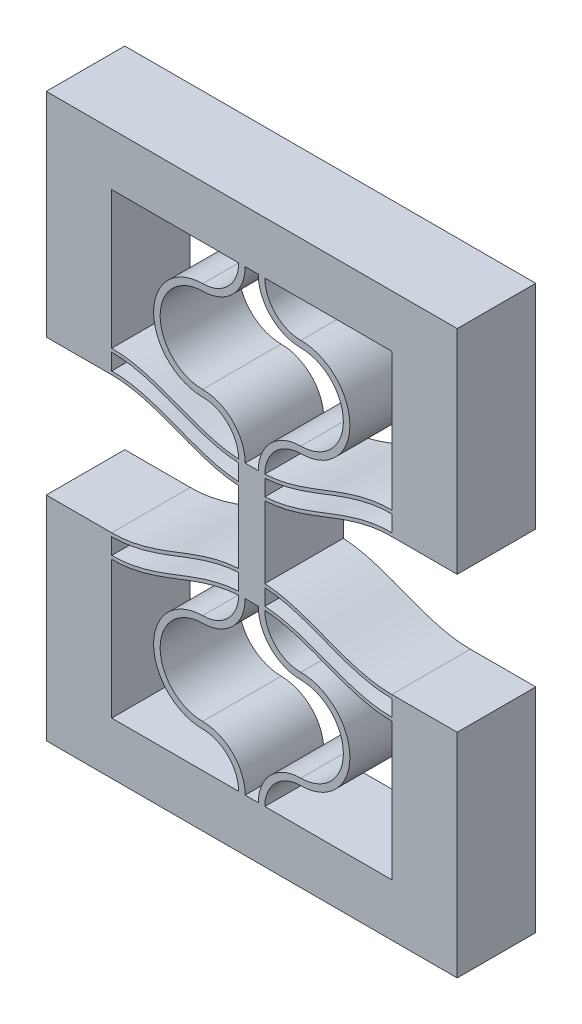
SolidWorks part; units mm, degrees
ref_plane "Front Plane" through (0, 0, 0) normal (0, 0, 1) x (1, 0, 0)
ref_plane "Top Plane" through (0, 0, 0) normal (0, 1, 0) x (1, 0, 0)
ref_plane "Right Plane" through (0, 0, 0) normal (1, 0, 0) x (0, 0, -1)
sketch "Sketch1" plane through (0, 0, 0) normal (0, 0, 1) x (1, 0, 0)
  line L4 (0, 10.5) -> (0, 0)
  line L5 (10.2, 0) -> (10.2, 13) construction
  line L6 (10.2, 13) -> (10.2, 15.9852) construction
  line L17 (9.7, 0) -> (0, 0)
  line L18 (10.7, 0) -> (20.4, 0)
  line L19 (20.4, 0) -> (20.4, 10.5)
  line L20 (10.7, 13.2452) -> (10.7, 14.4852)
  line L21 (9.7, 13.2452) -> (9.7, 14.4852)
  line L22 (10.7, 14.7452) -> (10.7, 15.9852)
  line L23 (10.7, 15.9852) -> (9.7, 15.9852)
  line L24 (9.7, 15.9852) -> (9.7, 14.7452)
  line L31 (-5, 12.26) -> (-5, -4)
  line L32 (-5, -4) -> (25.4, -4)
  line L33 (25.4, -4) -> (25.4, 12.26)
  line L34 (0, 10.76) -> (0, 12)
  line L36 (-5, 12.26) -> (0, 12.26)
  line L37 (25.4, 12.26) -> (20.4, 12.26)
  line L38 (20.4, 10.76) -> (20.4, 12)
  arc A0 (10.2, 13) -> (6.95, 9.75) centre (6.95, 13) cw
  arc A1 (6.95, 9.75) -> (6.95, 3.25) centre (6.95, 6.5) ccw
  arc A2 (6.95, 3.25) -> (10.2, 0) centre (6.95, 0) cw
  arc A3 (9.7, 12.9852) -> (6.95, 10.25) centre (6.95, 13) cw
  arc A4 (6.95, 10.25) -> (6.95, 2.75) centre (6.95, 6.5) ccw
  arc A5 (6.95, 2.75) -> (9.7, 0) centre (6.95, 0) cw
  arc A6 (9.7, 13) -> (6.95, 10.25) centre (6.95, 13) cw construction
  arc A7 (13.45, 3.25) -> (10.2, 0) centre (13.45, 0) ccw
  arc A8 (13.45, 2.75) -> (10.7, 0) centre (13.45, 0) ccw
  arc A9 (13.45, 9.75) -> (13.45, 3.25) centre (13.45, 6.5) cw
  arc A10 (13.45, 10.25) -> (13.45, 2.75) centre (13.45, 6.5) cw
  arc A11 (10.7, 12.9852) -> (13.45, 10.25) centre (13.45, 13) ccw
  arc A12 (10.2, 13) -> (13.45, 9.75) centre (13.45, 13) ccw
  spline S0 degree 4 poles (-2.0399, 10.9987) (-1.9769, 10.9844) (-1.8506, 10.9568) (-1.6594, 10.9185) (-1.4063, 10.8738) (-1.1473, 10.836) (-0.8994, 10.8056) (-0.6275, 10.7825) (-0.4084, 10.7671) (-0.0945, 10.7598) (0.0489, 10.7593) (0.3554, 10.7653) (0.5833, 10.7785) (0.8327, 10.7992) (1.1232, 10.8326) (1.4148, 10.8743) (1.7521, 10.9345) (2.2064, 11.0333) (2.726, 11.1697) (3.2397, 11.3281) (3.7479, 11.5024) (4.1845, 11.6613) (4.5513, 11.7992) (4.9172, 11.9395) (5.2828, 12.0805) (5.7402, 12.2559) (6.427, 12.5125) (7.2136, 12.7819) (8.1107, 13.0284) (9.0261, 13.1932) (9.8075, 13.2661) (10.5925, 13.2661) (11.3739, 13.1932) (12.2893, 13.0284) (13.1864, 12.7819) (13.973, 12.5125) (14.6598, 12.2559) (15.2087, 12.0455) (15.6656, 11.8688) (16.1235, 11.6948) (16.6521, 11.5024) (17.1603, 11.3281) (17.6739, 11.1697) (18.1937, 11.0333) (18.5999, 10.9449) (18.8889, 10.8915) (19.1309, 10.8534) (19.3251, 10.827) (19.5196, 10.8048) (19.7158, 10.7868) (19.909, 10.7733) (20.1017, 10.7642) (20.3513, 10.7593) (20.4943, 10.7598) (20.8085, 10.7671) (21.0274, 10.7825) (21.2994, 10.8056) (21.5473, 10.836) (21.8063, 10.8738) (22.0594, 10.9185) (22.2506, 10.9568) (22.3769, 10.9844) (22.4399, 10.9987) knots 0 0 0 0 0 0.010251 0.020502 0.030753 0.041005 0.05113 0.061255 0.071381 0.081506 0.089265 0.097024 0.112543 0.120302 0.128061 0.143579 0.159098 0.174616 0.201648 0.22868 0.244198 0.259716 0.275235 0.290753 0.306271 0.32179 0.352826 0.40689 0.437927 0.468963 0.5 0.531037 0.562073 0.59311 0.647174 0.67821 0.693729 0.709247 0.740284 0.755802 0.77132 0.798352 0.825384 0.840902 0.856421 0.86418 0.871939 0.879698 0.887457 0.895217 0.902976 0.910735 0.918494 0.928619 0.938745 0.94887 0.958995 0.969247 0.979498 0.989749 1 1 1 1 1 construction
  spline S1 degree 4 poles (0, 10.76) (0.041, 10.76) (0.1243, 10.7608) (0.3554, 10.7653) (0.5833, 10.7785) (0.8327, 10.7992) (1.1232, 10.8326) (1.4148, 10.8743) (1.7521, 10.9345) (2.2064, 11.0333) (2.726, 11.1697) (3.2397, 11.3281) (3.7479, 11.5024) (4.1845, 11.6613) (4.5513, 11.7992) (4.9172, 11.9395) (5.2828, 12.0805) (5.7402, 12.2559) (6.427, 12.5125) (7.2136, 12.7819) (8.1107, 13.0284) (9.0261, 13.1932) (9.8075, 13.2661) (10.5925, 13.2661) (11.3739, 13.1932) (12.2893, 13.0284) (13.1864, 12.7819) (13.973, 12.5125) (14.6598, 12.2559) (15.2087, 12.0455) (15.6656, 11.8688) (16.1235, 11.6948) (16.6521, 11.5024) (17.1603, 11.3281) (17.6739, 11.1697) (18.1937, 11.0333) (18.5999, 10.9449) (18.8889, 10.8915) (19.1309, 10.8534) (19.3251, 10.827) (19.5196, 10.8048) (19.7158, 10.7868) (19.909, 10.7733) (20.1017, 10.7642) (20.2757, 10.7608) (20.359, 10.76) (20.4, 10.76) knots 0.081506 0.081506 0.081506 0.081506 0.081506 0.089265 0.097024 0.112543 0.120302 0.128061 0.143579 0.159098 0.174616 0.201648 0.22868 0.244198 0.259716 0.275235 0.290753 0.306271 0.32179 0.352826 0.40689 0.437927 0.468963 0.5 0.531037 0.562073 0.59311 0.647174 0.67821 0.693729 0.709247 0.740284 0.755802 0.77132 0.798352 0.825384 0.840902 0.856421 0.86418 0.871939 0.879698 0.887457 0.895217 0.902976 0.910735 0.918494 0.918494 0.918494 0.918494 0.918494
  spline S2 degree 4 poles (-2.0399, 12.2387) (-1.9769, 12.2244) (-1.8506, 12.1968) (-1.6594, 12.1585) (-1.4063, 12.1138) (-1.1473, 12.076) (-0.8994, 12.0456) (-0.6275, 12.0225) (-0.4084, 12.0071) (-0.0945, 11.9998) (0.0489, 11.9993) (0.3554, 12.0053) (0.5833, 12.0185) (0.8327, 12.0392) (1.1232, 12.0726) (1.4148, 12.1143) (1.7521, 12.1745) (2.2064, 12.2733) (2.726, 12.4097) (3.2397, 12.5681) (3.7479, 12.7424) (4.1845, 12.9013) (4.5513, 13.0392) (4.9172, 13.1795) (5.2828, 13.3205) (5.7402, 13.4959) (6.427, 13.7525) (7.2136, 14.0219) (8.1107, 14.2684) (9.0261, 14.4332) (9.8075, 14.5061) (10.5925, 14.5061) (11.3739, 14.4332) (12.2893, 14.2684) (13.1864, 14.0219) (13.973, 13.7525) (14.6598, 13.4959) (15.2087, 13.2855) (15.6656, 13.1088) (16.1235, 12.9348) (16.6521, 12.7424) (17.1603, 12.5681) (17.6739, 12.4097) (18.1937, 12.2733) (18.5999, 12.1849) (18.8889, 12.1315) (19.1309, 12.0934) (19.3251, 12.067) (19.5196, 12.0448) (19.7158, 12.0268) (19.909, 12.0133) (20.1017, 12.0042) (20.3513, 11.9993) (20.4943, 11.9998) (20.8085, 12.0071) (21.0274, 12.0225) (21.2994, 12.0456) (21.5473, 12.076) (21.8063, 12.1138) (22.0594, 12.1585) (22.2506, 12.1968) (22.3769, 12.2244) (22.4399, 12.2387) knots 0 0 0 0 0 0.010251 0.020502 0.030753 0.041005 0.05113 0.061255 0.071381 0.081506 0.089265 0.097024 0.112543 0.120302 0.128061 0.143579 0.159098 0.174616 0.201648 0.22868 0.244198 0.259716 0.275235 0.290753 0.306271 0.32179 0.352826 0.40689 0.437927 0.468963 0.5 0.531037 0.562073 0.59311 0.647174 0.67821 0.693729 0.709247 0.740284 0.755802 0.77132 0.798352 0.825384 0.840902 0.856421 0.86418 0.871939 0.879698 0.887457 0.895217 0.902976 0.910735 0.918494 0.928619 0.938745 0.94887 0.958995 0.969247 0.979498 0.989749 1 1 1 1 1 construction
  spline S3 degree 4 poles (0, 12) (0.041, 12) (0.1243, 12.0008) (0.3554, 12.0053) (0.5833, 12.0185) (0.8327, 12.0392) (1.1232, 12.0726) (1.4148, 12.1143) (1.7521, 12.1745) (2.2064, 12.2733) (2.726, 12.4097) (3.2397, 12.5681) (3.7479, 12.7424) (4.1845, 12.9013) (4.5513, 13.0392) (4.9172, 13.1795) (5.2828, 13.3205) (5.7402, 13.4959) (6.427, 13.7525) (7.2136, 14.0219) (8.1107, 14.2684) (9.0261, 14.4332) (9.8075, 14.5061) (10.5925, 14.5061) (11.3739, 14.4332) (12.2893, 14.2684) (13.1864, 14.0219) (13.973, 13.7525) (14.6598, 13.4959) (15.2087, 13.2855) (15.6656, 13.1088) (16.1235, 12.9348) (16.6521, 12.7424) (17.1603, 12.5681) (17.6739, 12.4097) (18.1937, 12.2733) (18.5999, 12.1849) (18.8889, 12.1315) (19.1309, 12.0934) (19.3251, 12.067) (19.5196, 12.0448) (19.7158, 12.0268) (19.909, 12.0133) (20.1017, 12.0042) (20.2757, 12.0008) (20.359, 12) (20.4, 12) knots 0.081506 0.081506 0.081506 0.081506 0.081506 0.089265 0.097024 0.112543 0.120302 0.128061 0.143579 0.159098 0.174616 0.201648 0.22868 0.244198 0.259716 0.275235 0.290753 0.306271 0.32179 0.352826 0.40689 0.437927 0.468963 0.5 0.531037 0.562073 0.59311 0.647174 0.67821 0.693729 0.709247 0.740284 0.755802 0.77132 0.798352 0.825384 0.840902 0.856421 0.86418 0.871939 0.879698 0.887457 0.895217 0.902976 0.910735 0.918494 0.918494 0.918494 0.918494 0.918494
  spline S4 degree 4 poles (-2.0399, 12.4987) (-1.9769, 12.4844) (-1.8506, 12.4568) (-1.6594, 12.4185) (-1.4063, 12.3738) (-1.1473, 12.336) (-0.8994, 12.3056) (-0.6275, 12.2825) (-0.4084, 12.2671) (-0.0945, 12.2598) (0.0489, 12.2593) (0.3554, 12.2653) (0.5833, 12.2785) (0.8327, 12.2992) (1.1232, 12.3326) (1.4148, 12.3743) (1.7521, 12.4345) (2.2064, 12.5333) (2.726, 12.6697) (3.2397, 12.8281) (3.7479, 13.0024) (4.1845, 13.1613) (4.5513, 13.2992) (4.9172, 13.4395) (5.2828, 13.5805) (5.7402, 13.7559) (6.427, 14.0125) (7.2136, 14.2819) (8.1107, 14.5284) (9.0261, 14.6932) (9.8075, 14.7661) (10.5925, 14.7661) (11.3739, 14.6932) (12.2893, 14.5284) (13.1864, 14.2819) (13.973, 14.0125) (14.6598, 13.7559) (15.2087, 13.5455) (15.6656, 13.3688) (16.1235, 13.1948) (16.6521, 13.0024) (17.1603, 12.8281) (17.6739, 12.6697) (18.1937, 12.5333) (18.5999, 12.4449) (18.8889, 12.3915) (19.1309, 12.3534) (19.3251, 12.327) (19.5196, 12.3048) (19.7158, 12.2868) (19.909, 12.2733) (20.1017, 12.2642) (20.3513, 12.2593) (20.4943, 12.2598) (20.8085, 12.2671) (21.0274, 12.2825) (21.2994, 12.3056) (21.5473, 12.336) (21.8063, 12.3738) (22.0594, 12.4185) (22.2506, 12.4568) (22.3769, 12.4844) (22.4399, 12.4987) knots 0 0 0 0 0 0.010251 0.020502 0.030753 0.041005 0.05113 0.061255 0.071381 0.081506 0.089265 0.097024 0.112543 0.120302 0.128061 0.143579 0.159098 0.174616 0.201648 0.22868 0.244198 0.259716 0.275235 0.290753 0.306271 0.32179 0.352826 0.40689 0.437927 0.468963 0.5 0.531037 0.562073 0.59311 0.647174 0.67821 0.693729 0.709247 0.740284 0.755802 0.77132 0.798352 0.825384 0.840902 0.856421 0.86418 0.871939 0.879698 0.887457 0.895217 0.902976 0.910735 0.918494 0.928619 0.938745 0.94887 0.958995 0.969247 0.979498 0.989749 1 1 1 1 1 construction
  spline S5 degree 4 poles (0, 12.26) (0.041, 12.26) (0.1243, 12.2608) (0.3554, 12.2653) (0.5833, 12.2785) (0.8327, 12.2992) (1.1232, 12.3326) (1.4148, 12.3743) (1.7521, 12.4345) (2.2064, 12.5333) (2.726, 12.6697) (3.2397, 12.8281) (3.7479, 13.0024) (4.1845, 13.1613) (4.5513, 13.2992) (4.9172, 13.4395) (5.2828, 13.5805) (5.7402, 13.7559) (6.427, 14.0125) (7.2136, 14.2819) (8.1107, 14.5284) (9.0261, 14.6932) (9.8075, 14.7661) (10.5925, 14.7661) (11.3739, 14.6932) (12.2893, 14.5284) (13.1864, 14.2819) (13.973, 14.0125) (14.6598, 13.7559) (15.2087, 13.5455) (15.6656, 13.3688) (16.1235, 13.1948) (16.6521, 13.0024) (17.1603, 12.8281) (17.6739, 12.6697) (18.1937, 12.5333) (18.5999, 12.4449) (18.8889, 12.3915) (19.1309, 12.3534) (19.3251, 12.327) (19.5196, 12.3048) (19.7158, 12.2868) (19.909, 12.2733) (20.1017, 12.2642) (20.2757, 12.2608) (20.359, 12.26) (20.4, 12.26) knots 0.081506 0.081506 0.081506 0.081506 0.081506 0.089265 0.097024 0.112543 0.120302 0.128061 0.143579 0.159098 0.174616 0.201648 0.22868 0.244198 0.259716 0.275235 0.290753 0.306271 0.32179 0.352826 0.40689 0.437927 0.468963 0.5 0.531037 0.562073 0.59311 0.647174 0.67821 0.693729 0.709247 0.740284 0.755802 0.77132 0.798352 0.825384 0.840902 0.856421 0.86418 0.871939 0.879698 0.887457 0.895217 0.902976 0.910735 0.918494 0.918494 0.918494 0.918494 0.918494
  spline S8 degree 4 poles (-2.0399, 10.7387) (-1.9769, 10.7244) (-1.8506, 10.6968) (-1.6594, 10.6585) (-1.4063, 10.6138) (-1.1473, 10.576) (-0.8994, 10.5456) (-0.6275, 10.5225) (-0.4084, 10.5071) (-0.0945, 10.4998) (0.0489, 10.4993) (0.3554, 10.5053) (0.5833, 10.5185) (0.8327, 10.5392) (1.1232, 10.5726) (1.4148, 10.6143) (1.7521, 10.6745) (2.2064, 10.7733) (2.726, 10.9097) (3.2397, 11.0681) (3.7479, 11.2424) (4.1845, 11.4013) (4.5513, 11.5392) (4.9172, 11.6795) (5.2828, 11.8205) (5.7402, 11.9959) (6.427, 12.2525) (7.2136, 12.5219) (8.1107, 12.7684) (9.0261, 12.9332) (9.8075, 13.0061) (10.5925, 13.0061) (11.3739, 12.9332) (12.2893, 12.7684) (13.1864, 12.5219) (13.973, 12.2525) (14.6598, 11.9959) (15.2087, 11.7855) (15.6656, 11.6088) (16.1235, 11.4348) (16.6521, 11.2424) (17.1603, 11.0681) (17.6739, 10.9097) (18.1937, 10.7733) (18.5999, 10.6849) (18.8889, 10.6315) (19.1309, 10.5934) (19.3251, 10.567) (19.5196, 10.5448) (19.7158, 10.5268) (19.909, 10.5133) (20.1017, 10.5042) (20.3513, 10.4993) (20.4943, 10.4998) (20.8085, 10.5071) (21.0274, 10.5225) (21.2994, 10.5456) (21.5473, 10.576) (21.8063, 10.6138) (22.0594, 10.6585) (22.2506, 10.6968) (22.3769, 10.7244) (22.4399, 10.7387) knots 0 0 0 0 0 0.010251 0.020502 0.030753 0.041005 0.05113 0.061255 0.071381 0.081506 0.089265 0.097024 0.112543 0.120302 0.128061 0.143579 0.159098 0.174616 0.201648 0.22868 0.244198 0.259716 0.275235 0.290753 0.306271 0.32179 0.352826 0.40689 0.437927 0.468963 0.5 0.531037 0.562073 0.59311 0.647174 0.67821 0.693729 0.709247 0.740284 0.755802 0.77132 0.798352 0.825384 0.840902 0.856421 0.86418 0.871939 0.879698 0.887457 0.895217 0.902976 0.910735 0.918494 0.928619 0.938745 0.94887 0.958995 0.969247 0.979498 0.989749 1 1 1 1 1 construction
  spline S9 degree 4 poles (0, 10.5) (0.041, 10.5) (0.1243, 10.5008) (0.3554, 10.5053) (0.5833, 10.5185) (0.8327, 10.5392) (1.1232, 10.5726) (1.4148, 10.6143) (1.7521, 10.6745) (2.2064, 10.7733) (2.726, 10.9097) (3.2397, 11.0681) (3.7479, 11.2424) (4.1845, 11.4013) (4.5513, 11.5392) (4.9172, 11.6795) (5.2828, 11.8205) (5.7402, 11.9959) (6.427, 12.2525) (7.2136, 12.5219) (8.1107, 12.7684) (9.0261, 12.9332) (9.8075, 13.0061) (10.5925, 13.0061) (11.3739, 12.9332) (12.2893, 12.7684) (13.1864, 12.5219) (13.973, 12.2525) (14.6598, 11.9959) (15.2087, 11.7855) (15.6656, 11.6088) (16.1235, 11.4348) (16.6521, 11.2424) (17.1603, 11.0681) (17.6739, 10.9097) (18.1937, 10.7733) (18.5999, 10.6849) (18.8889, 10.6315) (19.1309, 10.5934) (19.3251, 10.567) (19.5196, 10.5448) (19.7158, 10.5268) (19.909, 10.5133) (20.1017, 10.5042) (20.2757, 10.5008) (20.359, 10.5) (20.4, 10.5) knots 0.081506 0.081506 0.081506 0.081506 0.081506 0.089265 0.097024 0.112543 0.120302 0.128061 0.143579 0.159098 0.174616 0.201648 0.22868 0.244198 0.259716 0.275235 0.290753 0.306271 0.32179 0.352826 0.40689 0.437927 0.468963 0.5 0.531037 0.562073 0.59311 0.647174 0.67821 0.693729 0.709247 0.740284 0.755802 0.77132 0.798352 0.825384 0.840902 0.856421 0.86418 0.871939 0.879698 0.887457 0.895217 0.902976 0.910735 0.918494 0.918494 0.918494 0.918494 0.918494
  dimension "D4" = 0.26
  dimension "D6" = 4
  dimension "D1" = 13
  dimension "D2" = 0.5
  dimension "D3" = 0.26
  dimension "D7" = 5
  dimension "D5" = 1.5
extrude "Boss-Extrude1" add sketch "Sketch1" along normal blind 6
sketch "Sketch4" plane through (0, 15.9852, 0) normal (0, 1, 0) x (1, 0, 0)
  line L24 (10.7, 0) -> (9.7, 0)
  line L25 (9.7, 0) -> (9.7, -6)
  line L26 (10.7, 0) -> (9.7, 0)
  line L27 (10.7, -6) -> (10.7, 0)
  line L29 (9.7, 0) -> (9.7, -6)
  line L31 (10.7, -6) -> (10.7, 0)
  line L32 (9.7, -6) -> (10.7, -6)
  line L33 (9.7, -6) -> (10.7, -6)
  dimension "D1" = 0
extrude "Boss-Extrude2" add sketch "Sketch4" along normal blind 1.5
mirror "Mirror3" about plane through (0, 17.4852, 0) normal (0, 1, 0) of bodies 179
ref_plane "Plane1" through (10.2, 0, 0) normal (-1, 0, 0) x (0, 0, 1)
split "Split2" trim tools "Plane1" bodies to split 247 102 resulting bodies 225
sketch "Sketch7" plane through (10.2, 0, 0) normal (-1, 0, 0) x (0, 0, 1)
  line L4 (6, 34.9704) -> (6, 38.9704)
  line L12 (0, 13) -> (6, 13)
  line L13 (0, 13) -> (6, 13)
  line L14 (6, 13) -> (6, 21.9704)
  line L15 (6, 13) -> (6, 21.9704)
  line L20 (6, 0) -> (0, 0)
  line L22 (6, 0) -> (0, 0)
  line L23 (0, -4) -> (6, -4)
  line L27 (0, -4) -> (6, -4)
  line L31 (6, 21.9704) -> (0, 21.9704)
  line L32 (6, 21.9704) -> (0, 21.9704)
  line L33 (0, 21.9704) -> (0, 13)
  line L34 (0, 21.9704) -> (0, 13)
  line L36 (6, -4) -> (6, 0)
  line L38 (6, 34.9704) -> (6, 38.9704)
  line L39 (6, 34.9704) -> (6, 38.9704)
  line L40 (6, 38.9704) -> (0, 38.9704)
  line L41 (6, 38.9704) -> (0, 38.9704)
  line L46 (6, 34.9704) -> (6, 38.9704)
  line L51 (0, 38.9704) -> (0, 34.9704)
  line L52 (0, 38.9704) -> (0, 34.9704)
  line L53 (0, 34.9704) -> (6, 34.9704)
  line L54 (0, 34.9704) -> (6, 34.9704)
  line L55 (6, 38.9704) -> (0, 38.9704)
  line L57 (6, 38.9704) -> (0, 38.9704)
  line L59 (6, -4) -> (6, 0)
  line L60 (0, 0) -> (0, -4)
  line L61 (0, 0) -> (0, -4)
  line L62 (0, 38.9704) -> (0, 34.9704)
  line L63 (0, 38.9704) -> (0, 34.9704)
  line L64 (0, 34.9704) -> (6, 34.9704)
  line L65 (0, 34.9704) -> (6, 34.9704)
  dimension "D1" = 0
  dimension "D2" = 0
  dimension "D3" = 0
  dimension "D4" = 0
extrude "Boss-Extrude3" add sketch "Sketch7" along normal blind 0.5
mirror "Mirror2" about plane through (9.7, 0, 0) normal (-1, 0, 0) of bodies 226
